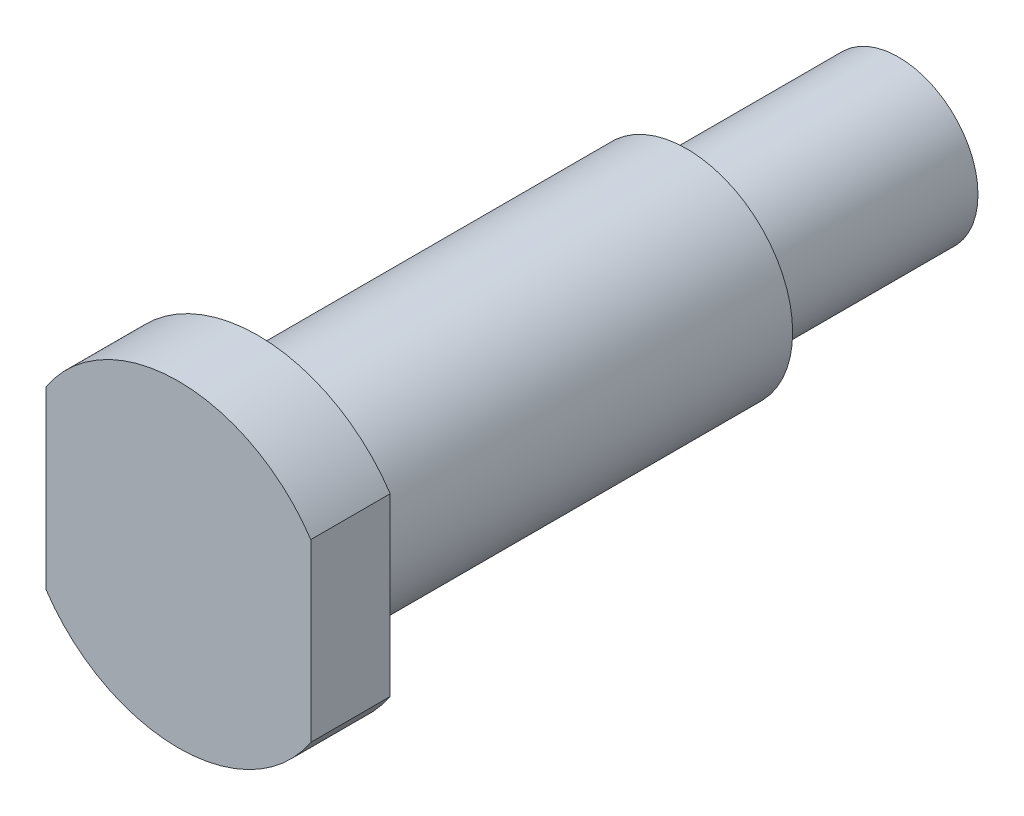
SolidWorks part; units mm, degrees
ref_plane "前视基准面" through (0, 0, 0) normal (0, 0, 1) x (1, 0, 0)
ref_plane "上视基准面" through (0, 0, 0) normal (0, 1, 0) x (1, 0, 0)
ref_plane "右视基准面" through (0, 0, 0) normal (1, 0, 0) x (0, 0, -1)
sketch "草图2" plane through (0, 0, 0) normal (1, 0, 0) x (0, 0, -1)
  line L0 (0, 0) -> (105.7683, 0) construction
  line L1 (0, 0) -> (0, 6)
  line L2 (0, 6) -> (3, 6)
  line L3 (3, 6) -> (3, 4)
  line L4 (3, 4) -> (19.2, 4)
  line L5 (19.2, 4) -> (19.2, 3)
  line L6 (0, 0) -> (27.2, 0)
  line L7 (19.2, 3) -> (27.2, 3)
  line L8 (27.2, 3) -> (27.2, 0)
  dimension "D1" = 12
  dimension "D2" = 16.2
  dimension "D3" = 3
  dimension "D4" = 8
  dimension "D5" = 6
  dimension "D6" = 8
revolve "旋转1" add sketch "草图2" angle 360 about L0
cosmetic thread "装饰螺纹线1" parameters "D2"=5
sketch "草图3" plane through (0, 0, 0) normal (0, 0, 1) x (1, 0, 0)
  line L1 (5, 6.5397) -> (-5, 6.5397)
  line L2 (5, 6.5397) -> (5, -6.5397)
  line L3 (5, -6.5397) -> (-5, -6.5397)
  line L4 (-5, 6.5397) -> (-5, -6.5397)
  line L5 (5, 6.5397) -> (-5, -6.5397) construction
  line L6 (5, -6.5397) -> (-5, 6.5397) construction
  point P0 (0, 0)
  dimension "D1" = 10
extrude "切除-拉伸1" cut sketch "草图3" against normal blind 10 flip side to cut
